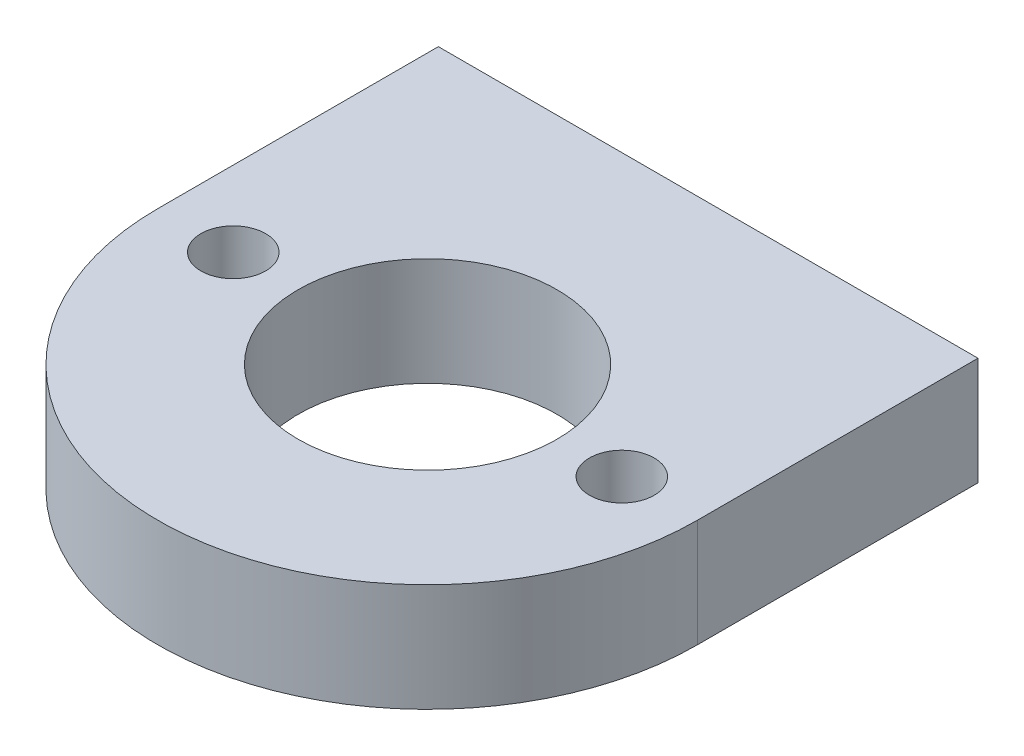
SolidWorks part; units mm, degrees
material "ｱｸﾘﾙ (中-上級の耐衝撃性)"
ref_plane "正面" through (0, 0, 0) normal (0, 0, 1) x (1, 0, 0)
ref_plane "平面" through (0, 0, 0) normal (0, 1, 0) x (1, 0, 0)
ref_plane "右側面" through (0, 0, 0) normal (1, 0, 0) x (0, 0, -1)
sketch "ｽｹｯﾁ1" plane through (0, 0, 0) normal (0, 0, 1) x (1, 0, 0)
  line L1 (-12.5, 2.5) -> (12.5, 2.5)
  line L2 (-12.5, 2.5) -> (-12.5, -2.5)
  line L3 (-12.5, -2.5) -> (12.5, -2.5)
  line L4 (12.5, 2.5) -> (12.5, -2.5)
  line L5 (-12.5, 2.5) -> (12.5, -2.5) construction
  line L6 (-12.5, -2.5) -> (12.5, 2.5) construction
  point P0 (0, 0)
  dimension "D1" = 5
  dimension "D2" = 25
extrude "ﾎﾞｽ - 押し出し1" add sketch "ｽｹｯﾁ1" along normal blind 13
sketch "ｽｹｯﾁ2" plane through (0, -2.5, 0) normal (0, -1, 0) x (1, 0, 0)
  line L0 (-12.5, 13) -> (12.5, 13) construction
  circle A0 centre (0, 13) radius 12.5
extrude "ﾎﾞｽ - 押し出し2" add sketch "ｽｹｯﾁ2" against normal blind 5
sketch "ｽｹｯﾁ3" plane through (0, 2.5, 0) normal (0, 1, 0) x (1, 0, 0)
  line L0 (12.5, -13) -> (-12.5, -13)
  circle A0 centre (0, -13) radius 6
  dimension "D1" = 12
extrude "ｶｯﾄ - 押し出し1" cut sketch "ｽｹｯﾁ3" against normal blind 5 contours L0 A0 | L0 A0
sketch "ｽｹｯﾁ4" plane through (0, 2.5, 0) normal (0, 1, 0) x (1, 0, 0)
  line L0 (0, -13) -> (-9, -13)
  line L1 (0, -13) -> (9, -13)
  circle A0 centre (0, -13) radius 9
  circle A1 centre (9, -13) radius 1.5
  circle A2 centre (-9, -13) radius 1.5
  dimension "D1" = 18
  dimension "D2" = 3
  dimension "D3" = 3
extrude "ｶｯﾄ - 押し出し2" cut sketch "ｽｹｯﾁ4" against normal blind 5 contours A1 | A2
sketch "ｽｹｯﾁ5" plane through (0, 0, 0) normal (0, 0, -1) x (-1, 0, 0)
  line L0 (0, 0) -> (9, 0)
  line L1 (0, 0) -> (-9, 0)
  dimension "D1" = 9
  dimension "D2" = 9
hole_wizard "M3x0.5 ねじ穴1" positions "ｽｹｯﾁ7" profile "ｽｹｯﾁ6" tap size "M3x0.5" standard "JIS"
sketch "ｽｹｯﾁ7" plane through (0, 0, 0) normal (0, 0, -1) x (-1, 0, 0)
  point P0 (-9, 0)
  point P3 (9, 0)
sketch "ｽｹｯﾁ6" plane through (9, 0, 0) normal (1, 0, 0) x (0, 1, 0)
  line L0 (0, 0) -> (0, 10.7511)
  line L1 (0, 10.7511) -> (1.25, 10)
  line L2 (1.25, 10) -> (1.25, 0)
  line L5 (1.25, 0) -> (0, 0)
  line L10 (0, 10.7511) -> (-1.25, 10) construction
  line L11 (0, -6.35) -> (0, 107.95) construction
  dimension "ねじ下穴ﾄﾞﾘﾙ直径" = 2.5
  dimension "ねじ下穴ﾄﾞﾘﾙの深さ" = 10
  dimension "ﾄﾞﾘﾙ角度" = 118
cosmetic thread "穴のねじ山1" parameters "D1"=7, "D2"=3
cosmetic thread "穴のねじ山2" parameters "D1"=7, "D2"=3
